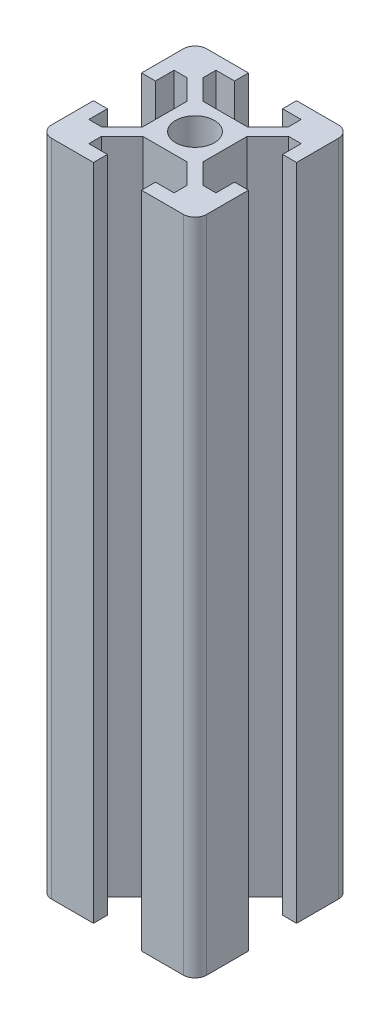
SolidWorks part; units mm, degrees
ref_plane "Płaszczyzna przednia" through (0, 0, 0) normal (0, 0, 1) x (1, 0, 0)
ref_plane "Płaszczyzna górna" through (0, 0, 0) normal (0, 1, 0) x (1, 0, 0)
ref_plane "Płaszczyzna prawa" through (0, 0, 0) normal (1, 0, 0) x (0, 0, -1)
sketch "Szkic1" plane through (0, 0, 0) normal (0, 1, 0) x (1, 0, 0)
  line L0 (0, 10) -> (0, -10) construction
  line L1 (-10, 0) -> (10, 0) construction
  line L2 (0, 3.9) -> (2.8393, 3.9)
  line L3 (3.9, 2.8393) -> (3.9, 0)
  line L4 (10, 3.1) -> (10, 8.5)
  line L5 (8.5, 10) -> (3.1, 10)
  line L6 (3.1, 10) -> (3.1, 8.2)
  line L7 (3.1, 8.2) -> (5.5, 8.2)
  line L8 (5.5, 8.2) -> (5.5, 6.5607)
  line L9 (5.5, 6.5607) -> (2.8393, 3.9)
  line L10 (3.9, 2.8393) -> (6.5607, 5.5)
  line L11 (6.5607, 5.5) -> (8.2, 5.5)
  line L12 (8.2, 5.5) -> (8.2, 3.1)
  line L13 (8.2, 3.1) -> (10, 3.1)
  line L14 (3.9, 0) -> (3.9, -2.8393)
  line L15 (2.8393, -3.9) -> (0, -3.9)
  line L16 (3.1, -10) -> (8.5, -10)
  line L17 (10, -8.5) -> (10, -3.1)
  line L18 (10, -3.1) -> (8.2, -3.1)
  line L19 (8.2, -3.1) -> (8.2, -5.5)
  line L20 (8.2, -5.5) -> (6.5607, -5.5)
  line L21 (6.5607, -5.5) -> (3.9, -2.8393)
  line L22 (2.8393, -3.9) -> (5.5, -6.5607)
  line L23 (5.5, -6.5607) -> (5.5, -8.2)
  line L24 (5.5, -8.2) -> (3.1, -8.2)
  line L25 (3.1, -8.2) -> (3.1, -10)
  line L26 (10, 0) -> (-10, 0) construction
  line L27 (0, 10) -> (0, -10) construction
  line L28 (0, -3.9) -> (-2.8393, -3.9)
  line L29 (-3.9, -2.8393) -> (-3.9, 0)
  line L30 (-10, -3.1) -> (-10, -8.5)
  line L31 (-8.5, -10) -> (-3.1, -10)
  line L32 (-3.1, -10) -> (-3.1, -8.2)
  line L33 (-3.1, -8.2) -> (-5.5, -8.2)
  line L34 (-5.5, -8.2) -> (-5.5, -6.5607)
  line L35 (-5.5, -6.5607) -> (-2.8393, -3.9)
  line L36 (-3.9, -2.8393) -> (-6.5607, -5.5)
  line L37 (-6.5607, -5.5) -> (-8.2, -5.5)
  line L38 (-8.2, -5.5) -> (-8.2, -3.1)
  line L39 (-8.2, -3.1) -> (-10, -3.1)
  line L40 (0, -10) -> (0, 10) construction
  line L41 (10, 0) -> (-10, 0) construction
  line L42 (-3.9, 0) -> (-3.9, 2.8393)
  line L43 (-2.8393, 3.9) -> (0, 3.9)
  line L44 (-3.1, 10) -> (-8.5, 10)
  line L45 (-10, 8.5) -> (-10, 3.1)
  line L46 (-10, 3.1) -> (-8.2, 3.1)
  line L47 (-8.2, 3.1) -> (-8.2, 5.5)
  line L48 (-8.2, 5.5) -> (-6.5607, 5.5)
  line L49 (-6.5607, 5.5) -> (-3.9, 2.8393)
  line L50 (-2.8393, 3.9) -> (-5.5, 6.5607)
  line L51 (-5.5, 6.5607) -> (-5.5, 8.2)
  line L52 (-5.5, 8.2) -> (-3.1, 8.2)
  line L53 (-3.1, 8.2) -> (-3.1, 10)
  line L54 (-10, 0) -> (10, 0) construction
  line L55 (0, -10) -> (0, 10) construction
  arc A0 (2.5, 0) -> (0, 2.5) centre (0, 0) ccw
  arc A1 (10, 8.5) -> (8.5, 10) centre (8.5, 8.5) ccw
  arc A2 (0, -2.5) -> (2.5, 0) centre (0, 0) ccw
  arc A3 (8.5, -10) -> (10, -8.5) centre (8.5, -8.5) ccw
  arc A4 (-2.5, 0) -> (0, -2.5) centre (0, 0) ccw
  arc A5 (-10, -8.5) -> (-8.5, -10) centre (-8.5, -8.5) ccw
  arc A6 (0, 2.5) -> (-2.5, 0) centre (0, 0) ccw
  arc A7 (-8.5, 10) -> (-10, 8.5) centre (-8.5, 8.5) ccw
  point P6 (0, 0)
  point P90 (0, 0)
  dimension "D2" = 45
  dimension "D3" = 2.5
  dimension "D7" = 1.5
  dimension "D1" = 20
  dimension "D4" = 6.1
  dimension "D5" = 11
  dimension "D6" = 6.2
  dimension "D8" = 1.8
  dimension "D9" = 1.5
  dimension "D10" = 4
extrude "Dodanie-wyciągnięcie1" add sketch "Szkic1" along normal blind 85 contours L44 A7 L45 L46 L47 L48 L49 L42 L29 L36 L37 L38 L39 L30 A5 L31 L32 L33 L34 L35 L28 L15 L22 L23 L24 L25 L16 A3 L17 L18 L19 L20 L21 L14 L3 L10 L11 L12 L13 L4 A1 L5 L6 L7 L8 L9 L2 L43 L50 L51 L52
